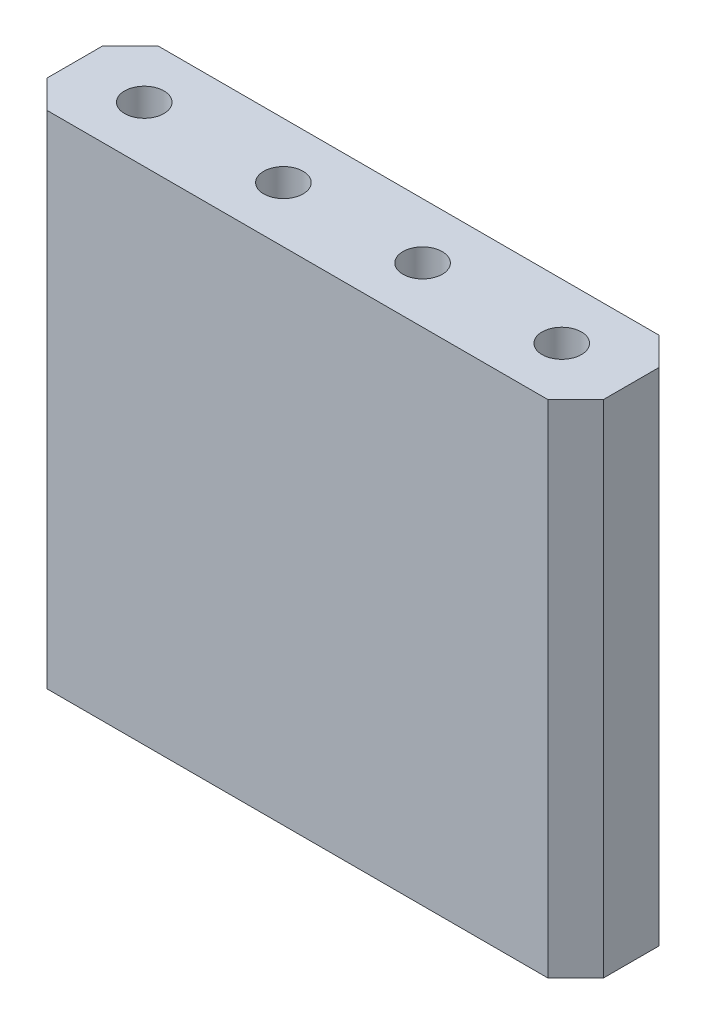
SolidWorks part; units mm, degrees
ref_plane "Спереди" through (0, 0, 0) normal (0, 0, 1) x (1, 0, 0)
ref_plane "Сверху" through (0, 0, 0) normal (0, 1, 0) x (1, 0, 0)
ref_plane "Справа" through (0, 0, 0) normal (1, 0, 0) x (0, 0, -1)
sketch "Эскиз1" plane through (0, 0, 0) normal (0, 1, 0) x (1, 0, 0)
  line L0 (-3.5, 0.25) -> (-3.5, -0.25)
  line L2 (-4, -0.25) -> (-4, 0.25)
  line L4 (4, -0.25) -> (4, 0.25)
  line L5 (-4, -0.25) -> (4, 0.25) construction
  line L6 (-4, 0.25) -> (4, -0.25) construction
  line L7 (-1.5, 0.25) -> (-1.5, -0.25)
  line L8 (-1, 0.25) -> (-1, -0.25)
  line L9 (1, 0.25) -> (1, -0.25)
  line L10 (3.5, 0.25) -> (3.5, -0.25)
  line L11 (1.5, 0.25) -> (1.5, -0.25)
  line L12 (-4, 0.25) -> (-3.5, 0.25)
  line L13 (-3.5, -0.25) -> (-4, -0.25)
  line L14 (-1.5, 0.25) -> (-1, 0.25)
  line L15 (-1, -0.25) -> (-1.5, -0.25)
  line L16 (1, -0.25) -> (1.5, -0.25)
  line L17 (1, 0.25) -> (1.5, 0.25)
  line L18 (3.5, -0.25) -> (4, -0.25)
  line L19 (3.5, 0.25) -> (4, 0.25)
  line L21 (-5, -1) -> (5, -1)
  line L22 (-5, -1) -> (-5, 1)
  line L23 (-5, 1) -> (5, 1)
  line L24 (5, -1) -> (5, 1)
  line L25 (-5, -1) -> (5, 1) construction
  line L26 (-5, 1) -> (5, -1) construction
  point P0 (0, 0)
  point P16 (0, 0)
  dimension "D1" = 0.5
  dimension "D2" = 2
  dimension "D3" = 0.5
  dimension "D4" = 2
  dimension "D5" = 0.5
  dimension "D6" = 2
  dimension "D7" = 8
  dimension "D8" = 0.5
  dimension "D9" = 10
  dimension "D10" = 2
extrude "Бобышка-Вытянуть1" add sketch "Эскиз1" along normal blind 7
sketch "Эскиз2" plane through (0, 7, 0) normal (0, 1, 0) x (1, 0, 0)
  line L0 (-4, 0) -> (-3.5, 0) construction
  line L1 (-5, -1) -> (5, -1)
  line L2 (-5, -1) -> (-5, 1)
  line L3 (-5, 1) -> (5, 1)
  line L4 (5, -1) -> (5, 1)
  line L5 (-5, -1) -> (5, 1) construction
  line L6 (-5, 1) -> (5, -1) construction
  line L7 (-4, 0.25) -> (-4, -0.25) construction
  line L8 (-3.5, -0.25) -> (-3.5, 0.25) construction
  line L9 (-1.5, 0) -> (-1, 0) construction
  line L10 (-1.5, 0.25) -> (-1.5, -0.25) construction
  line L11 (-1, -0.25) -> (-1, 0.25) construction
  line L12 (1, 0) -> (1.5, 0) construction
  line L13 (1, 0.25) -> (1, -0.25) construction
  line L14 (1.5, -0.25) -> (1.5, 0.25) construction
  line L15 (3.5, 0) -> (4, 0) construction
  line L16 (3.5, 0.25) -> (3.5, -0.25) construction
  line L17 (4, -0.25) -> (4, 0.25) construction
  circle A0 centre (-3.75, 0) radius 0.3536
  circle A1 centre (-1.25, 0) radius 0.3536
  circle A2 centre (1.25, 0) radius 0.3536
  circle A3 centre (3.75, 0) radius 0.3536
  point P0 (0, 0)
extrude "Бобышка-Вытянуть2" add sketch "Эскиз2" along normal blind 2
chamfer "Фаска1" distance 0.5 angle 45 4 edges at (-5, 4.5, 1) (-5, 4.5, -1) (5, 4.5, 1) (5, 4.5, -1)
